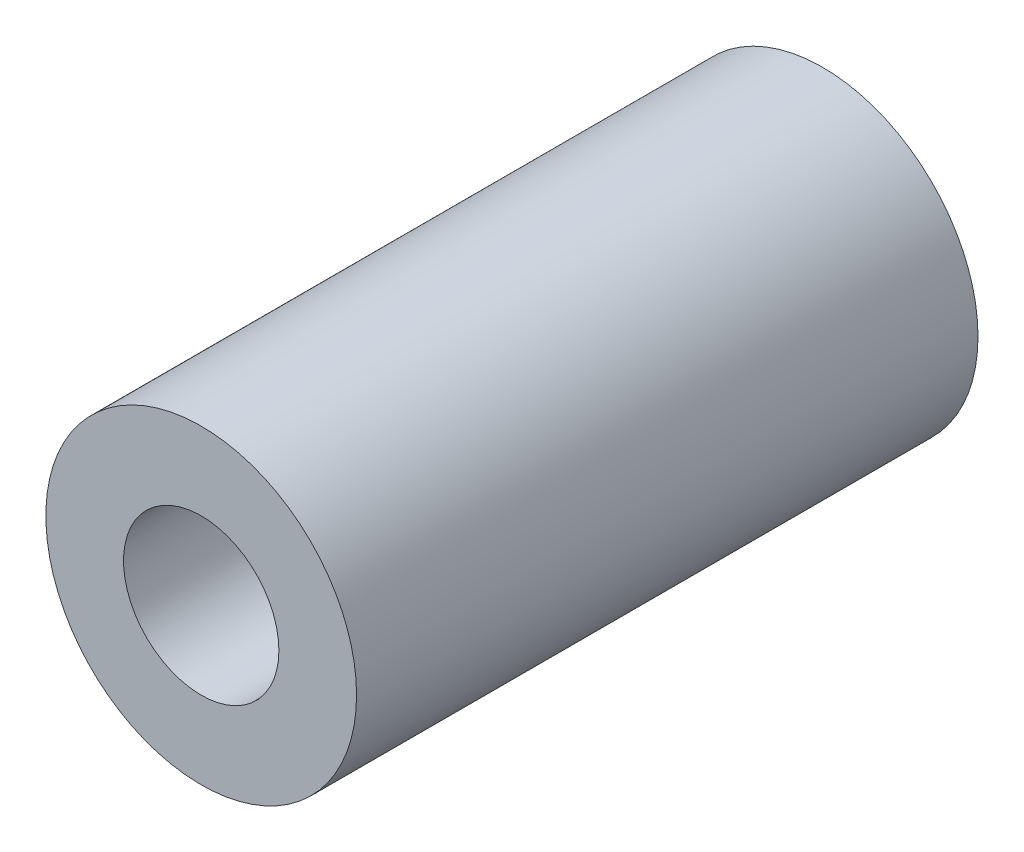
SolidWorks part; units mm, degrees
material "6061 合金"
ref_plane "前视基准面" through (0, 0, 0) normal (0, 0, 1) x (1, 0, 0)
ref_plane "上视基准面" through (0, 0, 0) normal (0, 1, 0) x (1, 0, 0)
ref_plane "右视基准面" through (0, 0, 0) normal (1, 0, 0) x (0, 0, -1)
sketch "草图1" plane through (0, 0, 0) normal (0, 0, 1) x (1, 0, 0)
  circle A1 centre (0, 0) radius 2.5
  dimension "D1" = 5
extrude "凸台-拉伸1" add sketch "草图1" along normal blind 10
hole_wizard "M3 螺纹孔1" positions "草图2" profile "草图3" tap size "M3" standard "GB" end condition through all
sketch "草图2" plane through (0, 0, 10) normal (0, 0, 1) x (1, 0, 0)
  point P0 (0, 0)
sketch "草图3" plane through (0, 0, 10) normal (1, 0, 0) x (0, -1, 0)
  line L0 (0, 0) -> (0, 10)
  line L1 (0, 10) -> (1.25, 10)
  line L2 (1.25, 10) -> (1.25, 0)
  line L5 (1.25, 0) -> (0, 0)
  line L11 (0, -6.35) -> (0, 107.95) construction
  dimension "通孔螺纹孔钻头直径" = 2.5
  dimension "通孔螺纹孔钻头深度" = 10
cosmetic thread "孔螺蚊线1"
